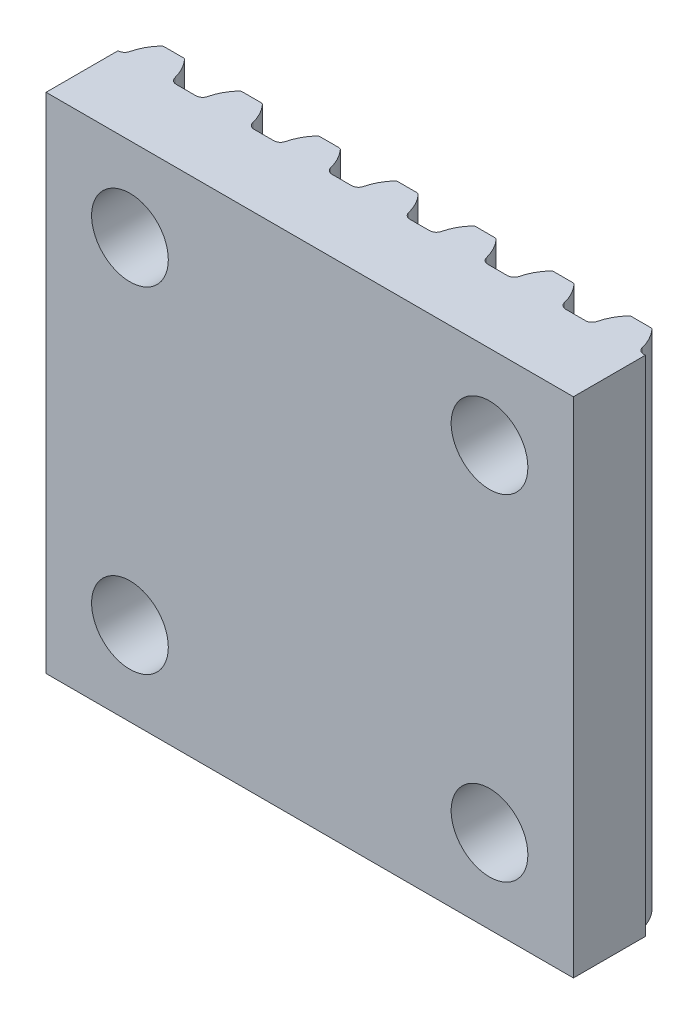
SolidWorks part; units mm, degrees
ref_plane "前基準面" through (0, 0, 0) normal (0, 0, 1) x (1, 0, 0)
ref_plane "上基準面" through (0, 0, 0) normal (0, 1, 0) x (1, 0, 0)
ref_plane "右基準面" through (0, 0, 0) normal (1, 0, 0) x (0, 0, -1)
sketch "草圖1" plane through (0, 0, 0) normal (0, 0, 1) x (1, 0, 0)
  line L1 (-11, -10.5) -> (11, -10.5)
  line L2 (-11, -10.5) -> (-11, 10.5)
  line L3 (-11, 10.5) -> (11, 10.5)
  line L4 (11, -10.5) -> (11, 10.5)
  line L5 (-11, -10.5) -> (11, 10.5) construction
  line L6 (-11, 10.5) -> (11, -10.5) construction
  point P0 (0, 0)
  dimension "D1" = 22
  dimension "D2" = 21
extrude "填料-伸長1" add sketch "草圖1" along normal blind 3
sketch "草圖3" plane through (0, -10.5, 0) normal (0, -1, 0) x (1, 0, 0)
  line L0 (-9.7841, 0.254) -> (-9.7841, -1.11) construction
  line L2 (-11, 3) -> (-11, 0) construction
  line L4 (-10.1718, -1.11) -> (-9.3965, -1.11)
  line L5 (-11, 0) -> (11, 0) construction
  line L6 (-10.7591, 0.254) -> (-8.8091, 0.254) construction
  line L7 (-11, 0) -> (-8.5683, 0)
  line L8 (-10.7591, 0.254) -> (-11, 0.254) construction
  line L9 (-8.8091, 0.254) -> (-8.5683, 0.254) construction
  line L10 (-8.5683, 0.254) -> (-8.5683, 0) construction
  arc A4 (-10.1718, -1.11) -> (-10.2838, -1.0598) centre (-10.1718, -0.96) cw
  arc A5 (-10.2838, -1.0598) -> (-10.728, -0.2137) centre (-8.8091, 0.254) cw
  arc A6 (-10.728, -0.2137) -> (-11, 0) centre (-11, -0.28) ccw
  arc A7 (-9.3965, -1.11) -> (-9.2845, -1.0598) centre (-9.3965, -0.96) ccw
  arc A8 (-9.2845, -1.0598) -> (-8.8403, -0.2137) centre (-10.7591, 0.254) ccw
  arc A9 (-8.8403, -0.2137) -> (-8.5683, 0) centre (-8.5683, -0.28) cw
  point P7 (-9.7841, -1.11)
  point P20 (-9.7841, 0.254)
  dimension "D2" = 1.975
  dimension "D3" = 1.95
  dimension "D1" = 0.15
  dimension "D5" = 0.28
  dimension "D4" = 1.364
  dimension "D6" = 0.2409
extrude "填料-伸長2" add sketch "草圖3" against normal up to surface (21 mm away) up to face at (0, 10.5, 1.5)
pattern_linear "直線複製排列4" count 7 spacing 3.25 along (1, 0, 0) of "填料-伸長2"
sketch "草圖2" plane through (0, 0, 3) normal (0, 0, 1) x (1, 0, 0)
  line L0 (0, 0) -> (-7.5, 0) construction
  line L1 (-7.5, 0) -> (-7.5, 7) construction
  circle A0 centre (-7.5, 7) radius 1.6
  dimension "D3" = 3.2
  dimension "D1" = 7.5
  dimension "D2" = 7
extrude "除料-伸長1" cut sketch "草圖2" against normal through all
pattern_linear "直線複製排列1" count 2 spacing 15 along (1, 0, 0) count 2 spacing 14 along (0, -1, 0) of "除料-伸長1"
